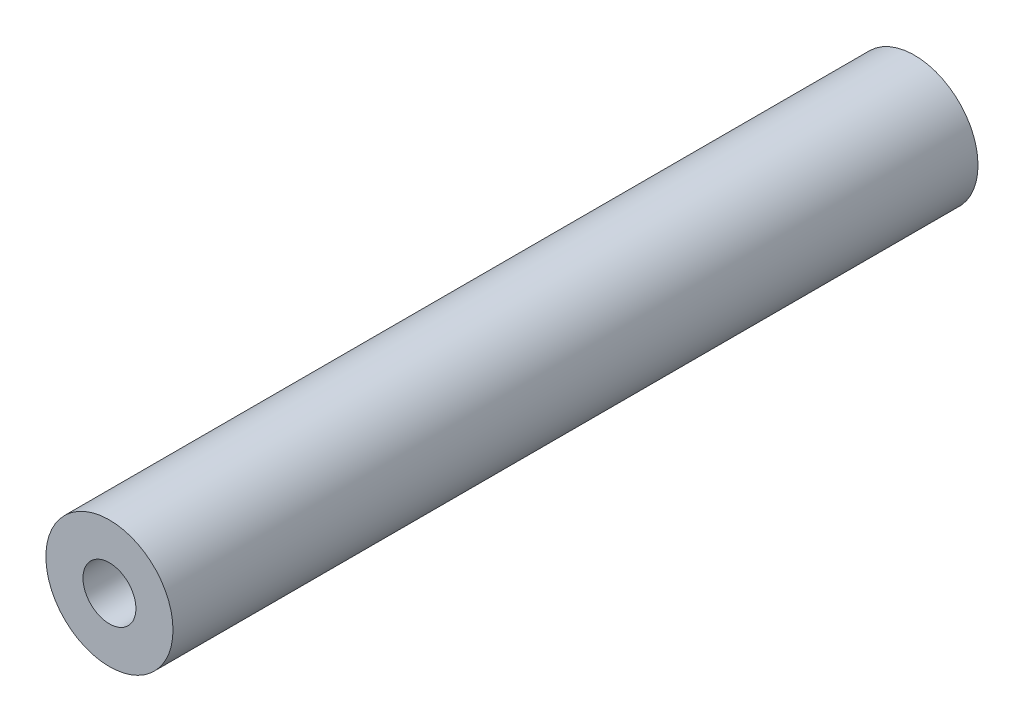
SolidWorks part; units mm, degrees
material "6061 合金"
ref_plane "前视基准面" through (0, 0, 0) normal (0, 0, 1) x (1, 0, 0)
ref_plane "上视基准面" through (0, 0, 0) normal (0, 1, 0) x (1, 0, 0)
ref_plane "右视基准面" through (0, 0, 0) normal (1, 0, 0) x (0, 0, -1)
sketch "草图1" plane through (0, 0, 0) normal (0, 0, 1) x (1, 0, 0)
  circle A1 centre (0, 0) radius 6
  dimension "D2" = 12
extrude "凸台-拉伸1" add sketch "草图1" along normal blind 76
hole_wizard "M6 螺纹孔1" positions "草图2" profile "草图3" tap size "M6" standard "ISO"
sketch "草图2" plane through (0, 0, 76) normal (0, 0, 1) x (1, 0, 0)
  point P0 (0, 0)
sketch "草图3" plane through (0, 0, 76) normal (1, 0, 0) x (0, -1, 0)
  line L0 (0, 0) -> (0, 34.5022)
  line L1 (0, 34.5022) -> (2.5, 33)
  line L2 (2.5, 33) -> (2.5, 0)
  line L5 (2.5, 0) -> (0, 0)
  line L10 (0, 34.5022) -> (-2.5, 33) construction
  line L11 (0, -6.35) -> (0, 107.95) construction
  dimension "螺纹孔钻头直径" = 5
  dimension "螺纹孔钻头深度" = 33
  dimension "导头角度" = 118
cosmetic thread "孔螺蚊线1" parameters "D1"=30, "D2"=6
hole_wizard "M6 螺纹孔2" positions "草图4" profile "草图5" tap size "M6" standard "ISO"
sketch "草图4" plane through (0, 0, 0) normal (0, 0, -1) x (-1, 0, 0)
  point P0 (0, 0)
sketch "草图5" plane through (0, 0, 0) normal (1, 0, 0) x (0, 1, 0)
  line L0 (0, 0) -> (0, 34.5022)
  line L1 (0, 34.5022) -> (2.5, 33)
  line L2 (2.5, 33) -> (2.5, 0)
  line L5 (2.5, 0) -> (0, 0)
  line L10 (0, 34.5022) -> (-2.5, 33) construction
  line L11 (0, -6.35) -> (0, 107.95) construction
  dimension "螺纹孔钻头直径" = 5
  dimension "螺纹孔钻头深度" = 33
  dimension "导头角度" = 118
cosmetic thread "孔螺蚊线2"
